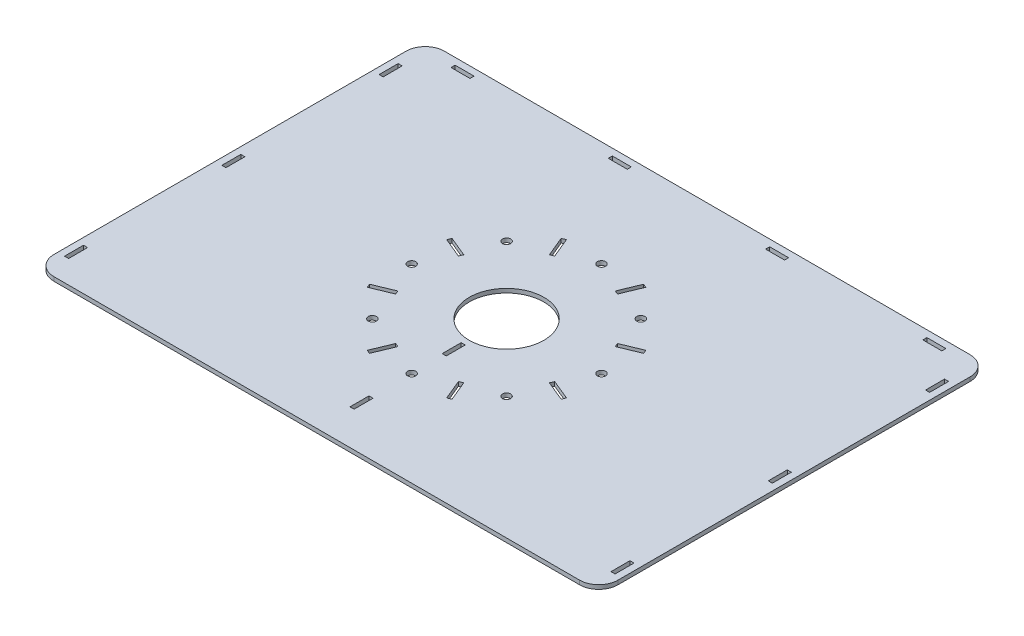
SolidWorks part; units mm, degrees
ref_plane "Front Plane" through (0, 0, 0) normal (0, 0, 1) x (1, 0, 0)
ref_plane "Top Plane" through (0, 0, 0) normal (0, 1, 0) x (1, 0, 0)
ref_plane "Right Plane" through (0, 0, 0) normal (1, 0, 0) x (0, 0, -1)
sketch "Sketch1" plane through (0, 0, 0) normal (0, 1, 0) x (1, 0, 0)
  line L0 (-193.8579, -140) -> (193.8579, -140)
  line L1 (-193.8579, 148) -> (193.8579, 148)
  line L2 (-208, 133.8579) -> (-208, -125.8579)
  line L4 (208, 133.8579) -> (208, -125.8579)
  arc A0 (-193.8579, 148) -> (-208, 133.8579) centre (-193.8579, 133.8579) ccw
  arc A1 (208, 133.8579) -> (193.8579, 148) centre (193.8579, 133.8579) ccw
  arc A2 (193.8579, -140) -> (208, -125.8579) centre (193.8579, -125.8579) ccw
  arc A3 (-208, -125.8579) -> (-193.8579, -140) centre (-193.8579, -125.8579) ccw
  point P0 (0, 0)
  point P4 (0, 0)
  dimension "D3" = 14.1421
  dimension "D5" = 14.1421
  dimension "D7" = 14.1421
  dimension "D9" = 14.1421
  dimension "D1" = 148
  dimension "D2" = 208
  dimension "D4" = 387.7157
  dimension "D6" = 259.7157
  dimension "D8" = 387.7157
  dimension "D10" = 133.8579
  dimension "D11" = 133.8579
  dimension "D12" = 125.8579
extrude "Boss-Extrude1" add sketch "Sketch1" along normal blind 3
sketch "Sketch2" plane through (0, 3, 0) normal (0, 1, 0) x (1, 0, 0)
  line L0 (-31.2278, 71.472) -> (-28.4561, 72.62)
  line L1 (-31.2278, 71.472) -> (-25.1048, 56.6899)
  line L2 (-25.1048, 56.6899) -> (-22.3332, 57.838)
  line L3 (-28.4561, 72.62) -> (-22.3332, 57.838)
  dimension "D3" = 3
  dimension "D4" = 6.1229
  dimension "D5" = 3
  dimension "D6" = 56.6899
  dimension "D7" = 25.1048
  dimension "D8" = 14.7821
  dimension "D9" = 14.7821
  dimension "D10" = 1.1481
  dimension "D11" = 2.7716
  dimension "D12" = 25.1048
sketch "Sketch3" plane through (0, 3, 0) normal (0, 1, 0) x (1, 0, 0)
  circle A0 centre (0, 0) radius 27.5
  dimension "D1" = 55
extrude "Cut-Extrude1" cut sketch "Sketch2" against normal blind 3
extrude "Cut-Extrude2" cut sketch "Sketch3" against normal blind 3
pattern_circular "CirPattern1" count 8 over 360 about axis through (0, 0, 0) along (0, 1, 0) of "Cut-Extrude1"
sketch "Sketch5" plane through (0, 3, 0) normal (0, 1, 0) x (1, 0, 0)
  circle A1 centre (0, 70) radius 3
  dimension "D1" = 6
  dimension "D2" = 0
  dimension "D3" = 70
extrude "Cut-Extrude4" cut sketch "Sketch5" against normal blind 3
pattern_circular "CirPattern2" count 8 over 360 about axis through (0, 0, 0) along (0, 1, 0) of "Cut-Extrude4"
sketch "Sketch6" plane through (0, 3, 0) normal (0, 1, 0) x (1, 0, 0)
  line L3 (181, 143) -> (181, 140)
  line L4 (-181, 143) -> (-167, 143)
  line L5 (-181, 143) -> (-181, 140)
  line L6 (-181, 140) -> (-167, 140)
  line L7 (-167, 143) -> (-167, 140)
  line L8 (181, 143) -> (167, 143)
  line L9 (167, 143) -> (167, 140)
  line L10 (181, 140) -> (167, 140)
  line L11 (65, 143) -> (65, 140)
  line L12 (-65, 143) -> (-51, 143)
  line L13 (-65, 143) -> (-65, 140)
  line L14 (-65, 140) -> (-51, 140)
  line L15 (-51, 143) -> (-51, 140)
  line L16 (65, 143) -> (51, 143)
  line L17 (51, 143) -> (51, 140)
  line L18 (65, 140) -> (51, 140)
  dimension "D1" = 14
  dimension "D2" = 3
  dimension "D3" = 167
  dimension "D4" = 140
  dimension "D5" = 14
  dimension "D6" = 3
  dimension "D7" = 140
  dimension "D8" = 51
  dimension "D9" = 14
  dimension "D10" = 3
  dimension "D11" = 14
  dimension "D12" = 3
  dimension "D13" = 140
  dimension "D14" = 51
  dimension "D15" = 140
  dimension "D16" = 167
extrude "Cut-Extrude7" cut sketch "Sketch6" against normal blind 3 contours L4 L7 L6 L5 | L12 L15 L14 L13 | L16 L17 L18 L11 | L8 L9 L10 L3
sketch "Sketch8" plane through (0, 3, 0) normal (0, 1, 0) x (1, 0, 0)
  line L3 (203, 123) -> (203, 109)
  line L4 (-203, 123) -> (-200, 123)
  line L5 (-203, 123) -> (-203, 109)
  line L6 (-203, 109) -> (-200, 109)
  line L7 (-200, 123) -> (-200, 109)
  line L8 (203, 123) -> (200, 123)
  line L9 (200, 123) -> (200, 109)
  line L10 (203, 109) -> (200, 109)
  line L11 (203, 7) -> (203, -7)
  line L12 (-203, 7) -> (-200, 7)
  line L13 (-203, 7) -> (-203, -7)
  line L14 (-203, -7) -> (-200, -7)
  line L15 (-200, 7) -> (-200, -7)
  line L16 (203, 7) -> (200, 7)
  line L17 (200, 7) -> (200, -7)
  line L18 (203, -7) -> (200, -7)
  line L19 (203, -123) -> (203, -109)
  line L20 (-203, -123) -> (-200, -123)
  line L21 (-203, -123) -> (-203, -109)
  line L22 (-203, -109) -> (-200, -109)
  line L23 (-200, -123) -> (-200, -109)
  line L24 (203, -123) -> (200, -123)
  line L25 (200, -123) -> (200, -109)
  line L26 (203, -109) -> (200, -109)
  dimension "D1" = 14
  dimension "D2" = 3
  dimension "D3" = 109
  dimension "D4" = 200
  dimension "D5" = 14
  dimension "D6" = 3
  dimension "D7" = 200
  dimension "D8" = 7
  dimension "D9" = 14
  dimension "D10" = 3
  dimension "D11" = 200
  dimension "D12" = 109
  dimension "D13" = 14
  dimension "D14" = 3
  dimension "D15" = 3
  dimension "D16" = 14
  dimension "D17" = 203
  dimension "D18" = 123
  dimension "D19" = 14
  dimension "D20" = 3
  dimension "D21" = 200
  dimension "D22" = 7
  dimension "D23" = 109
  dimension "D24" = 200
extrude "Cut-Extrude8" cut sketch "Sketch8" against normal blind 3
sketch "Sketch9" plane through (0, 3, 0) normal (0, 1, 0) x (1, 0, 0)
  text T0 "BOXX1" font "Century Gothic" height in points 22
  dimension "D1" = 35
  dimension "D2" = 12
sketch "Sketch10" plane through (0, 3, 0) normal (0, 1, 0) x (1, 0, 0)
  line L1 (-1.5, -46) -> (1.5, -46)
  line L2 (-1.5, -46) -> (-1.5, -32)
  line L3 (-1.5, -32) -> (1.5, -32)
  line L4 (1.5, -46) -> (1.5, -32)
  line L5 (-1.5, -46) -> (1.5, -32) construction
  line L6 (-1.5, -32) -> (1.5, -46) construction
  line L7 (-1.5, -114) -> (1.5, -114)
  line L8 (-1.5, -114) -> (-1.5, -100)
  line L9 (-1.5, -100) -> (1.5, -100)
  line L10 (1.5, -114) -> (1.5, -100)
  line L11 (-1.5, -114) -> (1.5, -100) construction
  line L12 (-1.5, -100) -> (1.5, -114) construction
  point P0 (0, -39)
  point P5 (0, -107)
  dimension "D1" = 14
  dimension "D2" = 3
  dimension "D3" = 32
  dimension "D4" = 1.5
  dimension "D5" = 100
  dimension "D6" = 1.5
  dimension "D7" = 14
  dimension "D8" = 3
extrude "Cut-Extrude9" cut sketch "Sketch10" against normal blind 3
